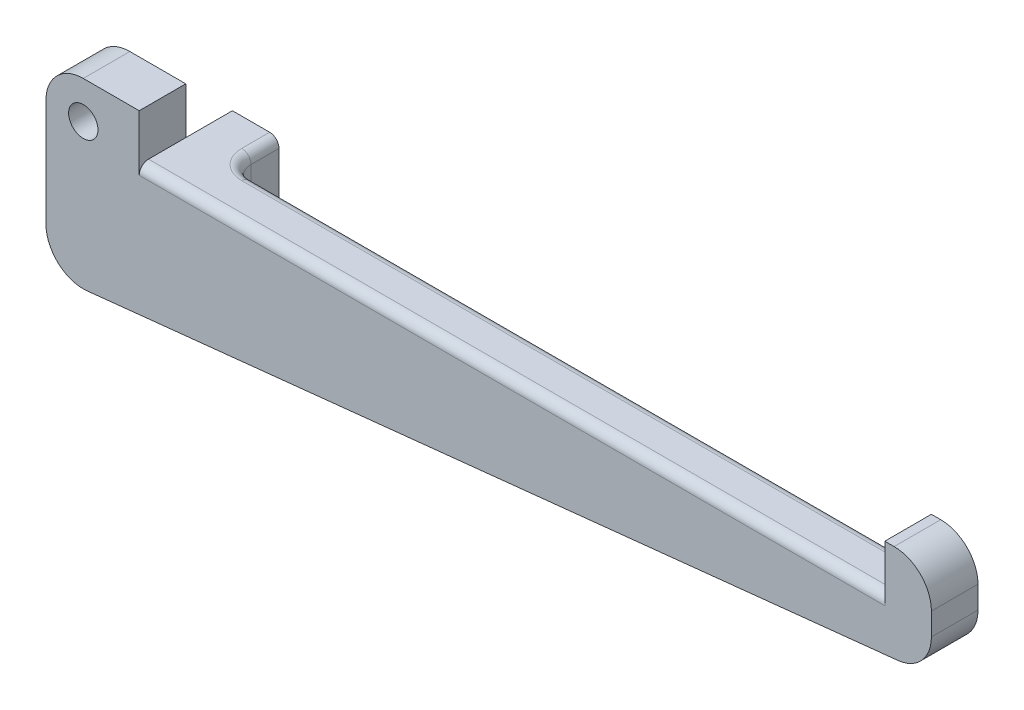
SolidWorks part; units mm, degrees
ref_plane "Front Plane" through (0, 0, 0) normal (0, 0, 1) x (1, 0, 0)
ref_plane "Top Plane" through (0, 0, 0) normal (0, 1, 0) x (1, 0, 0)
ref_plane "Right Plane" through (0, 0, 0) normal (1, 0, 0) x (0, 0, -1)
sketch "Sketch1" plane through (0, 0, 0) normal (0, 0, 1) x (1, 0, 0)
  line L0 (0, 0) -> (0, 7.62)
  line L1 (5.08, 12.7) -> (12.7, 12.7)
  line L2 (12.7, 12.7) -> (12.7, 6.35)
  line L3 (12.7, 6.35) -> (114.3, 6.35)
  line L4 (114.3, 6.35) -> (114.3, 12.7)
  line L5 (114.3, 12.7) -> (115.57, 12.7)
  line L6 (120.65, 7.62) -> (120.65, 4.5733)
  line L7 (116.1018, -0.4788) -> (5.6118, -12.1093)
  line L8 (0, -7.0572) -> (0, 0)
  arc A0 (5.6118, -12.1093) -> (0, -7.0572) centre (5.08, -7.0572) cw
  arc A1 (115.57, 12.7) -> (120.65, 7.62) centre (115.57, 7.62) cw
  arc A2 (120.65, 4.5733) -> (116.1018, -0.4788) centre (115.57, 4.5733) cw
  arc A3 (0, 7.62) -> (5.08, 12.7) centre (5.08, 7.62) cw
  point P12 (0, -12.7)
  point P15 (120.65, 12.7)
  point P18 (120.65, 0)
  point P21 (0, 12.7)
  dimension "D8" = 5.08
  dimension "D9" = 5.08
  dimension "D1" = 101.6
  dimension "D2" = 12.7
  dimension "D3" = 6.35
  dimension "D4" = 6.35
  dimension "D5" = 12.7
  dimension "D6" = 12.7
  dimension "D7" = 12.7
extrude "Boss-Extrude1" add sketch "Sketch1" along normal blind 6.35
sketch "Sketch2" plane through (0, 0, 0) normal (0, 0, -1) x (-1, 0, 0)
  line L0 (-12.7, 6.35) -> (-12.7, -6.35)
  line L1 (-12.7, 6.35) -> (-19.05, 6.35)
  line L2 (-12.7, -6.35) -> (-19.05, -6.35)
  line L3 (-19.05, 6.35) -> (-19.05, -6.35)
  dimension "D1" = 6.35
  dimension "D2" = 12.7
extrude "Boss-Extrude2" add sketch "Sketch2" along normal blind 6.35
fillet "Fillet1" radius 2.54 1 edges
fillet "Fillet2" radius 1.27 4 edges at (19.7939, 6.35, -0.7439) (63.5, 6.35, 6.35)
sketch "Sketch3" plane through (0, 0, 0) normal (0, 0, -1) x (-1, 0, 0)
  circle A0 centre (-5.08, 7.62) radius 2
  arc A1 (0, 7.62) -> (-5.08, 12.7) centre (-5.08, 7.62) ccw construction
  dimension "D1" = 4
extrude "Cut-Extrude1" cut sketch "Sketch3" against normal blind 6.35
